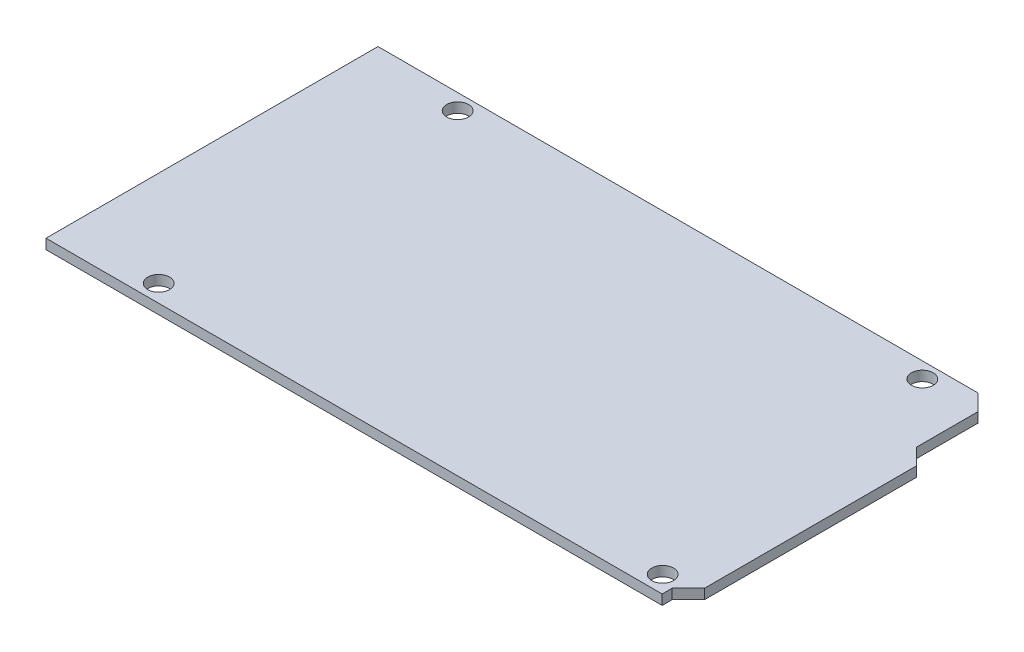
SolidWorks part; units mm, degrees
ref_plane "Front Plane" through (0, 0, 0) normal (0, 0, 1) x (1, 0, 0)
ref_plane "Top Plane" through (0, 0, 0) normal (0, 1, 0) x (1, 0, 0)
ref_plane "Right Plane" through (0, 0, 0) normal (1, 0, 0) x (0, 0, -1)
sketch "Sketch2" plane through (0, 0, 0) normal (0, 1, 0) x (1, 0, 0)
  line L0 (50.8, -22.47) -> (50.8, 11.5869)
  line L1 (48.2, -26.67) -> (-50.8, -26.67)
  line L2 (45.6, 26.67) -> (-50.8, 26.67)
  line L3 (-50.8, -26.67) -> (-50.8, 26.67)
  line L4 (50.8, -26.67) -> (-50.8, 26.67) construction
  line L5 (0, 0) -> (-50.8, -26.67) construction
  line L6 (48.2, 24.07) -> (48.2, 14.1869)
  line L8 (50.8, 11.5869) -> (48.2, 14.1869)
  line L9 (45.6, 26.67) -> (48.2, 24.07)
  line L12 (48.2, -25.07) -> (50.8, -22.47)
  line L13 (48.2, -25.07) -> (48.2, -26.67)
  point P1 (0, 0)
  dimension "D1" = 101.6
  dimension "D2" = 53.34
  dimension "D3" = 99
  dimension "D4" = 1.6
  dimension "D5" = 135
  dimension "D6" = 2.6
  dimension "D7" = 2.6
  dimension "D8" = 45
extrude "Boss-Extrude1" add sketch "Sketch2" along normal blind 1.6
hole_wizard "Ø3.5 (3.5) Diameter Hole1" positions "Sketch5" profile "Sketch4" hole size "Ø3.5" standard "Ansi Metric"
sketch "Sketch5" plane through (0, 1.6, 0) normal (0, 1, 0) x (-1, 0, 0)
  point P0 (35.4684, -24.1323)
  point P2 (35.4684, 23.8989)
  point P4 (-45.5029, 23.8989)
  point P6 (-39.1955, -24.1323)
sketch "Sketch4" plane through (-35.4684, 1.6, -24.1323) normal (1, 0, 0) x (0, 0, 1)
  line L0 (0, 0) -> (0, 4.0515)
  line L1 (0, 4.0515) -> (1.75, 3)
  line L2 (1.75, 3) -> (1.75, 0)
  line L5 (1.75, 0) -> (0, 0)
  line L10 (0, 4.0515) -> (-1.75, 3) construction
  line L11 (0, -6.35) -> (0, 107.95) construction
  dimension "Hole Dia." = 3.5
  dimension "Hole Depth" = 3
  dimension "Drill Angle" = 118
